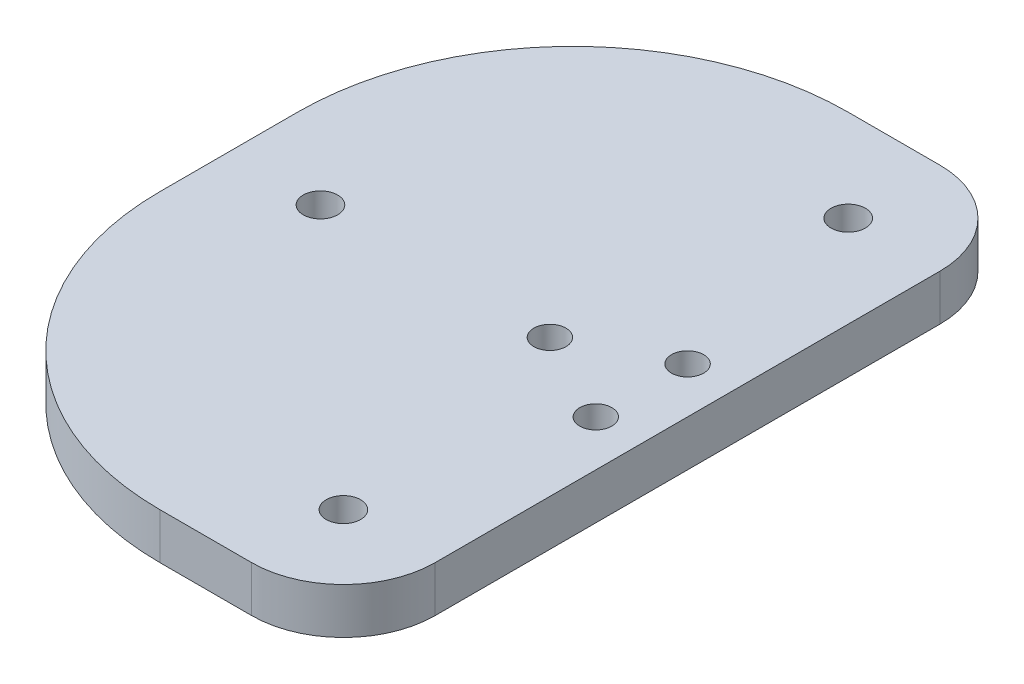
SolidWorks part; units mm, degrees
ref_plane "Front Plane" through (0, 0, 0) normal (0, 0, 1) x (1, 0, 0)
ref_plane "Top Plane" through (0, 0, 0) normal (0, 1, 0) x (1, 0, 0)
ref_plane "Right Plane" through (0, 0, 0) normal (1, 0, 0) x (0, 0, -1)
sketch "Sketch1" plane through (0, 0, 0) normal (0, 1, 0) x (1, 0, 0)
  line L0 (0, 37.5) -> (50, 37.5) construction
  line L1 (0, 0) -> (50, 0)
  line L2 (0, 0) -> (0, 75)
  line L3 (0, 75) -> (50, 75)
  line L4 (50, 0) -> (50, 75)
  circle A0 centre (40, 65) radius 1.875
  circle A1 centre (40, 10) radius 1.875
  circle A2 centre (10, 37.5) radius 1.875
  circle A3 centre (45, 42.5) radius 1.75
  circle A4 centre (45, 32.5) radius 1.75
  circle A5 centre (35, 37.5) radius 1.75
  dimension "D3" = 3.75
  dimension "D10" = 3.5
  dimension "D1" = 75
  dimension "D2" = 50
  dimension "D4" = 10
  dimension "D5" = 10
  dimension "D6" = 10
  dimension "D7" = 5
  dimension "D8" = 15
  dimension "D9" = 5
extrude "Boss-Extrude1" add sketch "Sketch1" along normal blind 5
sketch "Sketch2" plane through (0, 0, 0) normal (0, -1, 0) x (1, 0, 0)
  circle A0 centre (45, -32.5) radius 3
  circle A1 centre (45, -42.5) radius 3
  circle A2 centre (35, -37.5) radius 3
  dimension "D1" = 6
extrude "Cut-Extrude1" cut sketch "Sketch2" against normal blind 2.5
fillet "Fillet1" radius 30 2 edges at (0, 2.5, -75) (0, 2.5, 0)
fillet "Fillet2" radius 10 2 edges at (50, 2.5, -75) (50, 2.5, 0)
